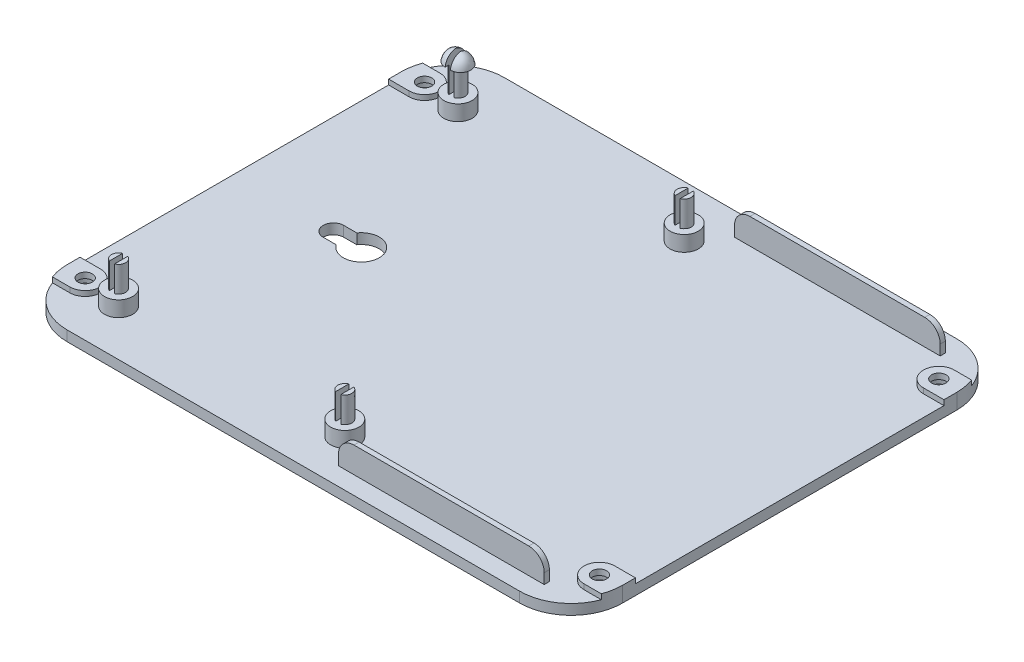
SolidWorks part; units mm, degrees
ref_plane "Front Plane" through (0, 0, 0) normal (0, 0, 1) x (1, 0, 0)
ref_plane "Top Plane" through (0, 0, 0) normal (0, 1, 0) x (1, 0, 0)
ref_plane "Right Plane" through (0, 0, 0) normal (1, 0, 0) x (0, 0, -1)
sketch "Sketch1" plane through (0, 0, 0) normal (0, 1, 0) x (1, 0, 0)
  line L0 (58.999, 8.4848) -> (96.6216, 8.4848) construction
  line L10 (-30.001, 50.9848) -> (57.999, 50.9848)
  line L11 (-40.001, 40.9848) -> (-40.001, -24.0152)
  line L12 (-30.001, -34.0152) -> (57.999, -34.0152)
  line L13 (67.999, 40.9848) -> (67.999, -24.0152)
  line L18 (-28.001, 48.9848) -> (55.999, 48.9848)
  line L19 (-38.001, 38.9848) -> (-38.001, -22.0152)
  line L20 (-28.001, -32.0152) -> (55.999, -32.0152)
  line L21 (65.999, 38.9848) -> (65.999, -22.0152)
  arc A12 (-40.001, 40.9848) -> (-30.001, 50.9848) centre (-30.001, 40.9848) cw
  arc A13 (-28.001, 48.9848) -> (-38.001, 38.9848) centre (-28.001, 38.9848) ccw
  arc A14 (67.999, -24.0152) -> (57.999, -34.0152) centre (57.999, -24.0152) cw
  arc A15 (65.999, -22.0152) -> (55.999, -32.0152) centre (55.999, -22.0152) cw
  arc A16 (67.999, 40.9848) -> (57.999, 50.9848) centre (57.999, 40.9848) ccw
  arc A17 (65.999, 38.9848) -> (55.999, 48.9848) centre (55.999, 38.9848) ccw
  arc A18 (-40.001, -24.0152) -> (-30.001, -34.0152) centre (-30.001, -24.0152) ccw
  arc A19 (-38.001, -22.0152) -> (-28.001, -32.0152) centre (-28.001, -22.0152) ccw
  point P0 (0, 0)
  point P6 (0, 0)
  point P29 (-28.001, 45.2348)
  point P31 (-28.001, 45.2348)
  point P35 (15.999, 45.2348)
  point P41 (15.999, -28.2652)
  point P47 (-28.001, -28.2652)
  dimension "D21" = 10
  dimension "D22" = 10
  dimension "D8" = 42.5
  dimension "D9" = 42.5
  dimension "D16" = 2
  dimension "D17" = 2
  dimension "D18" = 2
  dimension "D19" = 2
sketch "Sketch3" plane through (0, 0, 0) normal (0, 1, 0) x (1, 0, 0)
  line L0 (-30.001, -34.0152) -> (57.999, -34.0152) construction
  line L1 (67.999, 40.9848) -> (67.999, -24.0152) construction
  line L2 (-30.001, 50.9848) -> (57.999, 50.9848) construction
  line L3 (-40.001, 40.9848) -> (-40.001, -24.0152) construction
  line L4 (-30.001, -34.0152) -> (57.999, -34.0152)
  line L5 (67.999, 40.9848) -> (67.999, -24.0152)
  line L6 (-30.001, 50.9848) -> (57.999, 50.9848)
  line L7 (-40.001, 40.9848) -> (-40.001, -24.0152)
  arc A0 (-40.001, -24.0152) -> (-30.001, -34.0152) centre (-30.001, -24.0152) ccw construction
  arc A1 (57.999, -34.0152) -> (67.999, -24.0152) centre (57.999, -24.0152) ccw construction
  arc A2 (67.999, 40.9848) -> (57.999, 50.9848) centre (57.999, 40.9848) ccw construction
  arc A3 (-30.001, 50.9848) -> (-40.001, 40.9848) centre (-30.001, 40.9848) ccw construction
  arc A4 (-40.001, -24.0152) -> (-30.001, -34.0152) centre (-30.001, -24.0152) ccw
  arc A5 (57.999, -34.0152) -> (67.999, -24.0152) centre (57.999, -24.0152) ccw
  arc A6 (67.999, 40.9848) -> (57.999, 50.9848) centre (57.999, 40.9848) ccw
  arc A7 (-30.001, 50.9848) -> (-40.001, 40.9848) centre (-30.001, 40.9848) ccw
  dimension "D1" = 88
  dimension "D2" = 65
extrude "Boss-Extrude2" add sketch "Sketch3" along normal blind 2
sketch "Sketch5" plane through (0, 0, 34.0152) normal (0, 1, 0) x (1, 0, 0)
  line L0 (13.999, 83) -> (13.999, 110.4401) construction
  line L1 (-36.001, 78.5) -> (-39.3685, 78.5)
  line L2 (-36.001, 72.5) -> (-40.001, 72.5)
  line L3 (-40.001, 75) -> (-40.001, 10) construction
  line L4 (63.999, 78.5) -> (67.3665, 78.5)
  line L5 (63.999, 72.5) -> (67.999, 72.5)
  line L8 (63.999, 12.5) -> (67.999, 12.5)
  line L9 (67.999, 10) -> (67.999, 75) construction
  line L10 (63.999, 6.5) -> (67.3665, 6.5)
  line L11 (-36.001, 12.5) -> (-40.001, 12.5)
  line L12 (-36.001, 6.5) -> (-39.3685, 6.5)
  line L13 (67.999, 10) -> (67.999, 12.5)
  line L14 (-40.001, 75) -> (-40.001, 72.5)
  line L15 (67.999, 72.5) -> (67.999, 75)
  line L16 (-40.001, 12.5) -> (-40.001, 10)
  arc A0 (-30.001, 85) -> (-40.001, 75) centre (-30.001, 75) ccw construction
  arc A1 (67.999, 75) -> (57.999, 85) centre (57.999, 75) ccw construction
  arc A2 (57.999, 0) -> (67.999, 10) centre (57.999, 10) ccw construction
  arc A4 (-36.001, 6.5) -> (-36.001, 12.5) centre (-36.001, 9.5) ccw
  arc A5 (63.999, 12.5) -> (63.999, 6.5) centre (63.999, 9.5) ccw
  arc A6 (63.999, 78.5) -> (63.999, 72.5) centre (63.999, 75.5) ccw
  arc A7 (-36.001, 72.5) -> (-36.001, 78.5) centre (-36.001, 75.5) ccw
  arc A9 (-40.001, 10) -> (-30.001, 0) centre (-30.001, 10) ccw construction
  arc A10 (67.999, 75) -> (67.3665, 78.5) centre (57.999, 75) ccw
  arc A11 (67.3665, 6.5) -> (67.999, 10) centre (57.999, 10) ccw
  arc A12 (-40.001, 10) -> (-39.3685, 6.5) centre (-30.001, 10) ccw
  arc A13 (-39.3685, 78.5) -> (-40.001, 75) centre (-30.001, 75) ccw
  dimension "D1" = 6
  dimension "D2" = 6
  dimension "D3" = 6
  dimension "D4" = 6
  dimension "D5" = 50
  dimension "D6" = 50
  dimension "D7" = 50
  dimension "D8" = 50
sketch "Sketch6" plane through (0, 2, 0) normal (0, 1, 0) x (1, 0, 0)
  line L0 (-40.001, 8.4848) -> (67.999, 8.4848) construction
  line L1 (-40.001, 40.9848) -> (-40.001, -24.0152) construction
  line L2 (67.999, -24.0152) -> (67.999, 40.9848) construction
  line L3 (-15.3091, 50.9848) -> (-15.3091, -34.0152) construction
  line L4 (57.999, 50.9848) -> (-30.001, 50.9848) construction
  line L5 (-30.001, -34.0152) -> (57.999, -34.0152) construction
  line L6 (-16.9035, 8.4848) -> (-16.9035, 10.4848) construction
  line L8 (-16.9035, 8.4848) -> (-16.9035, 6.4848) construction
  line L9 (-16.9035, 8.4848) -> (-20.7218, 8.4848) construction
  line L10 (-18.1821, 6.4858) -> (-20.7218, 6.4858)
  line L11 (-18.1821, 10.4838) -> (-20.7218, 10.4838)
  arc A0 (-18.1821, 6.4858) -> (-18.1821, 10.4838) centre (-15.3091, 8.4848) ccw
  arc A2 (-20.7218, 10.4838) -> (-20.7218, 6.4858) centre (-20.7218, 8.4848) ccw
  point P16 (-18.8126, 8.4848)
  dimension "D1" = 7
  dimension "D2" = 2
  dimension "D3" = 2
  dimension "D4" = 1.5944
extrude "Cut-Extrude2" cut sketch "Sketch6" against normal blind 7 contours L11 A2 L10 A0
sketch "Sketch10" plane through (0, 0, 0) normal (0, 1, 0) x (1, 0, 0)
  line L0 (19.2632, 46.4848) -> (59.2632, 46.4848)
  line L1 (59.2632, 46.4848) -> (59.2632, 47.4848)
  line L2 (59.2632, 47.4848) -> (19.2632, 47.4848)
  line L3 (19.2632, 47.4848) -> (19.2632, 46.4848)
  line L4 (19.2632, -29.5152) -> (59.2632, -29.5152)
  line L5 (59.2632, -29.5152) -> (59.2632, -30.5152)
  line L6 (59.2632, -30.5152) -> (19.2632, -30.5152)
  line L7 (19.2632, -30.5152) -> (19.2632, -29.5152)
  line L8 (60.2632, 8.4848) -> (81.8858, 8.4848) construction
  dimension "D1" = 1
  dimension "D2" = 1
  dimension "D3" = 38
  dimension "D4" = 38
extrude "Boss-Extrude3" add sketch "Sketch10" along normal blind 7
sketch "Sketch12" plane through (0, 0, 30.5152) normal (0, 0, 1) x (1, 0, 0)
  line L0 (56.2632, 7) -> (59.2632, 7)
  line L1 (59.2632, 7) -> (59.2632, 2) construction
  line L2 (19.2632, 7) -> (59.2632, 7) construction
  line L3 (59.2632, 7) -> (59.2632, 4)
  line L4 (19.2632, 4) -> (19.2632, 7)
  line L5 (19.2632, 7) -> (19.2632, 2) construction
  line L6 (19.2632, 7) -> (22.2632, 7)
  arc A0 (59.2632, 4) -> (56.2632, 7) centre (56.2632, 4) ccw
  arc A1 (19.2632, 4) -> (22.2632, 7) centre (22.2632, 4) cw
  dimension "D2" = 3
extrude "Cut-Extrude4" cut sketch "Sketch12" against normal up to surface (1 mm away) up to face at (39.2632, 4.5, 29.5152)
sketch "Sketch13" plane through (0, 0, -47.4848) normal (0, 0, -1) x (-1, 0, 0)
  line L0 (-56.2632, 7) -> (-59.2632, 7)
  line L1 (-59.2632, 7) -> (-19.2632, 7) construction
  line L2 (-59.2632, 7) -> (-59.2632, 4)
  line L3 (-19.2632, 4) -> (-19.2632, 7)
  line L4 (-19.2632, 7) -> (-19.2632, 2) construction
  line L5 (-19.2632, 7) -> (-22.2632, 7)
  arc A0 (-19.2632, 4) -> (-22.2632, 7) centre (-22.2632, 4) ccw construction
  arc A1 (-56.2632, 7) -> (-59.2632, 4) centre (-56.2632, 4) ccw construction
  arc A2 (-19.2632, 4) -> (-22.2632, 7) centre (-22.2632, 4) ccw
  arc A3 (-56.2632, 7) -> (-59.2632, 4) centre (-56.2632, 4) ccw
extrude "Cut-Extrude5" cut sketch "Sketch13" against normal up to surface (1 mm away) up to face at (39.2632, 4.5, -46.4848)
sketch "Sketch14" plane through (0, 0, 0) normal (0, -1, 0) x (1, 0, 0)
  circle A0 centre (-29.011, 25.0118) radius 1.375
  circle A1 centre (14.9819, 25.0118) radius 1.375
  circle A2 centre (14.9819, -40.9882) radius 1.375
  circle A3 centre (-29.011, -40.9882) radius 1.375
  dimension "D1" = 2.75
extrude "Boss-Extrude4" add sketch "Sketch14" against normal blind 10 contours A0 | A1 | A2 | A3
sketch "Sketch15" plane through (0, 0, 0) normal (0, -1, 0) x (1, 0, 0)
  circle A0 centre (-29.011, 25.0118) radius 2.75
  circle A1 centre (14.9819, 25.0118) radius 2.75
  circle A2 centre (14.9819, -40.9882) radius 2.75
  circle A3 centre (-29.011, -40.9882) radius 2.75
  dimension "D1" = 5.5
extrude "Boss-Extrude5" add sketch "Sketch15" against normal up to surface (5 mm away)
ref_plane "Plane1" through (-29, 0, 0) normal (1, 0, 0) x (0, 0, -1)
extrude "Boss-Extrude8" add sketch "Sketch5" along normal blind 3
sketch "Sketch21" plane through (0, 0, 0) normal (0, -1, 0) x (1, 0, 0)
  circle A0 centre (-36.001, 24.5152) radius 3
  circle A1 centre (63.999, 24.5152) radius 3
  circle A2 centre (63.999, -41.4848) radius 3
  circle A3 centre (-36.001, -41.4848) radius 3
extrude "Cut-Extrude7" cut sketch "Sketch21" against normal blind 1.9
sketch "Sketch22" plane through (0, 1.9, 0) normal (0, -1, 0) x (1, 0, 0)
  circle A0 centre (-36.001, 24.5152) radius 1.4
  circle A1 centre (63.999, 24.5152) radius 1.4
  circle A2 centre (63.999, -41.4848) radius 1.4
  circle A3 centre (-36.001, -41.4848) radius 1.4
  dimension "D1" = 2.8
extrude "Cut-Extrude8" cut sketch "Sketch22" against normal blind 15
sketch "Sketch24" plane through (0, 10, 0) normal (0, 1, 0) x (1, 0, 0)
  line L1 (-29.511, 42.6974) -> (-28.511, 42.6974)
  line L2 (-29.511, 42.6974) -> (-29.511, 39.2791)
  line L3 (-29.511, 39.2791) -> (-28.511, 39.2791)
  line L4 (-28.511, 42.6974) -> (-28.511, 39.2791)
  line L5 (-29.511, 42.6974) -> (-28.511, 39.2791) construction
  line L6 (-29.511, 39.2791) -> (-28.511, 42.6974) construction
  line L7 (14.4819, 42.5751) -> (15.4819, 42.5751)
  line L8 (14.4819, 42.5751) -> (14.4819, 39.4014)
  line L9 (14.4819, 39.4014) -> (15.4819, 39.4014)
  line L10 (15.4819, 42.5751) -> (15.4819, 39.4014)
  line L11 (14.4819, 42.5751) -> (15.4819, 39.4014) construction
  line L12 (14.4819, 39.4014) -> (15.4819, 42.5751) construction
  line L13 (14.4819, -23.4125) -> (15.4819, -23.4125)
  line L14 (14.4819, -23.4125) -> (14.4819, -26.611)
  line L15 (14.4819, -26.611) -> (15.4819, -26.611)
  line L16 (15.4819, -23.4125) -> (15.4819, -26.611)
  line L17 (14.4819, -23.4125) -> (15.4819, -26.611) construction
  line L18 (14.4819, -26.611) -> (15.4819, -23.4125) construction
  line L19 (-29.511, -23.4125) -> (-28.511, -23.4125)
  line L20 (-29.511, -23.4125) -> (-29.511, -26.611)
  line L21 (-29.511, -26.611) -> (-28.511, -26.611)
  line L22 (-28.511, -23.4125) -> (-28.511, -26.611)
  line L23 (-29.511, -23.4125) -> (-28.511, -26.611) construction
  line L24 (-29.511, -26.611) -> (-28.511, -23.4125) construction
  point P0 (-29.011, 40.9882)
  point P5 (0, 0)
  point P6 (14.9819, 40.9882)
  point P11 (14.9819, -25.0118)
  point P16 (-29.011, -25.0118)
  dimension "D1" = 1
  dimension "D2" = 1
  dimension "D3" = 1
  dimension "D4" = 1
extrude "Cut-Extrude10" cut sketch "Sketch24" against normal up to surface (5 mm away) up to face at (-29.011, 5, -42.3632)
sketch "Sketch27" plane through (-29.511, 0, 0) normal (1, 0, 0) x (0, 0, -1)
  line L0 (40.9882, 10) -> (40.9882, 12.1427) construction
  line L1 (42.2691, 10) -> (39.7074, 10) construction
  line L2 (40.9882, 10) -> (42.9882, 10)
  line L3 (40.9882, 10) -> (40.9882, 12.1427)
  spline S0 degree 2 poles (42.9882, 10) (42.7019, 11.8057) (40.9882, 12.1427) knots 0 0 0 1 1 1
  dimension "D1" = 2
revolve "Revolve1" add sketch "Sketch27" angle 180 about L0
sketch "Sketch28" plane through (-28.511, 0, 0) normal (-1, 0, 0) x (0, 0, 1)
  line L0 (-40.9882, 12.1427) -> (-40.9882, 10)
  line L1 (-42.9882, 10) -> (-38.9882, 10) construction
  line L3 (-42.9882, 10) -> (-38.9882, 10)
  line L4 (-40.9882, 10) -> (-38.9882, 10)
  parabola Q2 (-38.9882, 10) -> (-40.9882, 12.1427) focus (-40.432, 10.7612) apex (-39.7029, 11.5114)
  parabola Q3 (-40.9882, 12.1427) -> (-42.9882, 10) focus (-41.5445, 10.7612) apex (-42.2736, 11.5114)
  parabola Q4 (-38.9882, 10) -> (-40.9882, 12.1427) focus (-40.432, 10.7612) apex (-39.7029, 11.5114)
  dimension "D1" = 0
revolve "Revolve2" add sketch "Sketch28" angle 180 about L0
